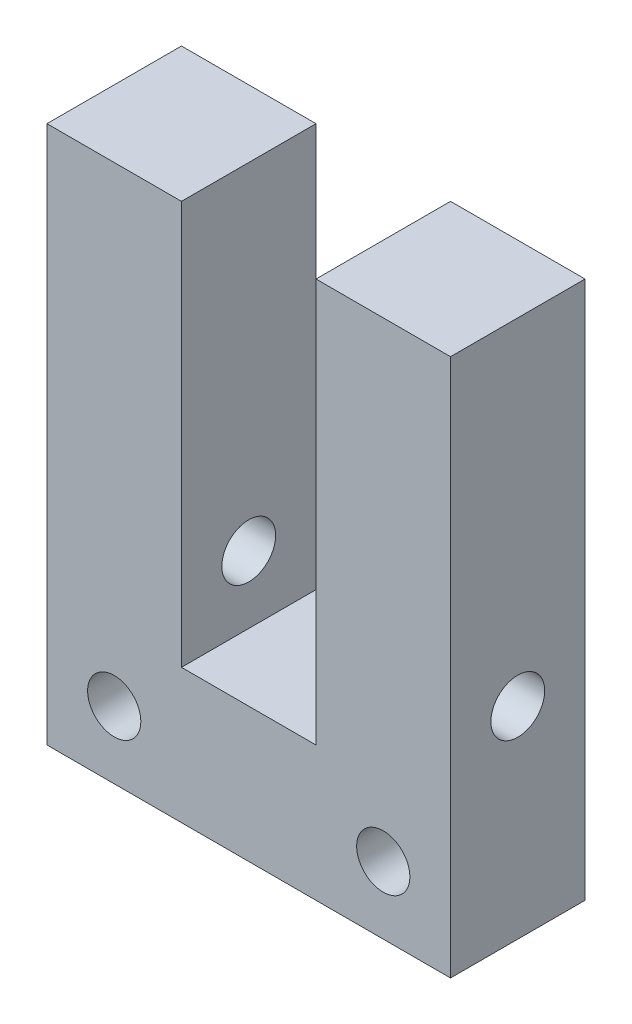
SolidWorks part; units mm, degrees
material "6061 Alloy"
ref_plane "Front Plane" through (0, 0, 0) normal (0, 0, 1) x (1, 0, 0)
ref_plane "Top Plane" through (0, 0, 0) normal (0, 1, 0) x (1, 0, 0)
ref_plane "Right Plane" through (0, 0, 0) normal (1, 0, 0) x (0, 0, -1)
sketch "Sketch1" plane through (0, 0, 0) normal (0, 0, 1) x (1, 0, 0)
  line L1 (0, 0) -> (19.05, 0)
  line L2 (0, 0) -> (0, 25.4)
  line L3 (0, 25.4) -> (19.05, 25.4)
  line L4 (19.05, 0) -> (19.05, 25.4)
  dimension "D1" = 19.05
  dimension "D2" = 25.4
extrude "Main block" add sketch "Sketch1" along normal blind 6.35
sketch "Sketch2" plane through (0, 0, 6.35) normal (0, 0, 1) x (1, 0, 0)
  line L0 (19.05, 25.4) -> (0, 25.4) construction
  line L1 (6.35, 6.35) -> (12.7, 6.35)
  line L2 (6.35, 6.35) -> (6.35, 25.4)
  line L3 (6.35, 25.4) -> (12.7, 25.4)
  line L4 (12.7, 6.35) -> (12.7, 25.4)
  line L6 (19.05, 0) -> (19.05, 25.4) construction
  dimension "D1" = 6.35
  dimension "D2" = 6.35
  dimension "D3" = 19.05
extrude "U-cut" cut sketch "Sketch2" against normal blind 12.7
sketch "Sketch3" plane through (0, 0, 6.35) normal (0, 0, 1) x (1, 0, 0)
  line L0 (0, 0) -> (19.05, 0) construction
  line L1 (19.05, 0) -> (19.05, 25.4) construction
  line L2 (0, 25.4) -> (0, 0) construction
  circle A0 centre (3.175, 3.175) radius 1.256
  circle A1 centre (15.875, 3.175) radius 1.256
  dimension "D3" = 2.5121
  dimension "D4" = 2.5121
  dimension "D1" = 3.175
  dimension "D2" = 3.175
  dimension "D5" = 3.175
  dimension "D6" = 3.175
extrude "Bolt holes" cut sketch "Sketch3" against normal blind 12.7
sketch "Sketch4" plane through (0, 0, 0) normal (-1, 0, 0) x (0, 0, 1)
  line L0 (0, 25.4) -> (0, 0) construction
  line L1 (6.35, 0) -> (0, 0) construction
  circle A0 centre (3.175, 9.525) radius 1.27
  dimension "D1" = 2.54
  dimension "D2" = 3.175
  dimension "D3" = 9.525
extrude "Pin hole" cut sketch "Sketch4" against normal through all
